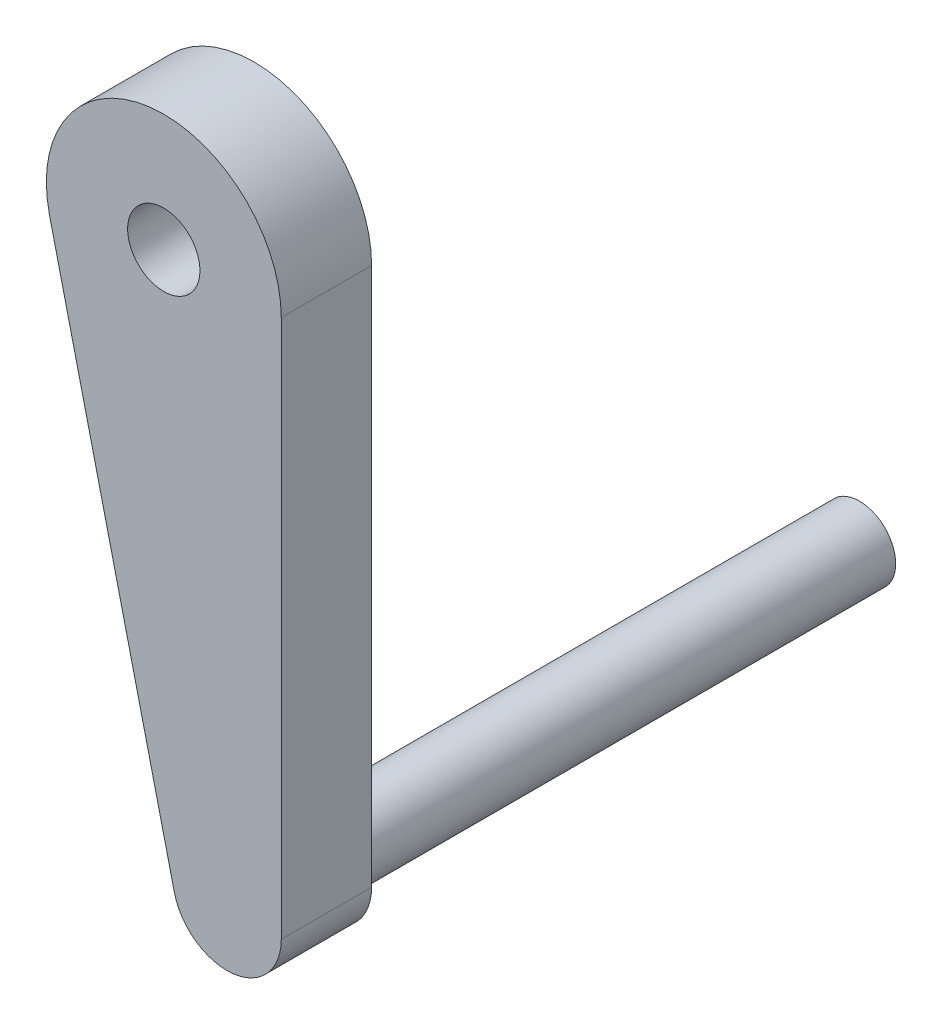
SolidWorks part; units mm, degrees
ref_plane "Front Plane" through (0, 0, 0) normal (0, 0, 1) x (1, 0, 0)
ref_plane "Top Plane" through (0, 0, 0) normal (0, 1, 0) x (1, 0, 0)
ref_plane "Right Plane" through (0, 0, 0) normal (1, 0, 0) x (0, 0, -1)
sketch "Sketch1" plane through (0, 0, 0) normal (0, 0, 1) x (1, 0, 0)
  line L0 (8.255, 0) -> (8.255, -37.8398)
  line L1 (0.7387, -38.7227) -> (-8.0303, -1.913)
  arc A0 (8.255, 0) -> (-8.0303, -1.913) centre (0, 0) ccw
  arc A1 (0.7387, -38.7227) -> (8.255, -37.8398) centre (4.445, -37.8398) ccw
  dimension "D1" = 16.51
  dimension "D2" = 7.62
  dimension "D3" = 38.1
extrude "Boss-Extrude1" add sketch "Sketch1" along normal blind 6.35
sketch "Sketch2" plane through (0, 0, 0) normal (0, 0, -1) x (-1, 0, 0)
  circle A0 centre (-4.445, -37.8398) radius 2.54
  dimension "D1" = 5.08
extrude "Boss-Extrude2" add sketch "Sketch2" along normal blind 38.1
sketch "Sketch3" plane through (0, 0, 6.35) normal (0, 0, 1) x (1, 0, 0)
  circle A0 centre (0, 0) radius 2.54
  dimension "D1" = 5.08
extrude "Cut-Extrude1" cut sketch "Sketch3" against normal blind 38.1 contours A0
